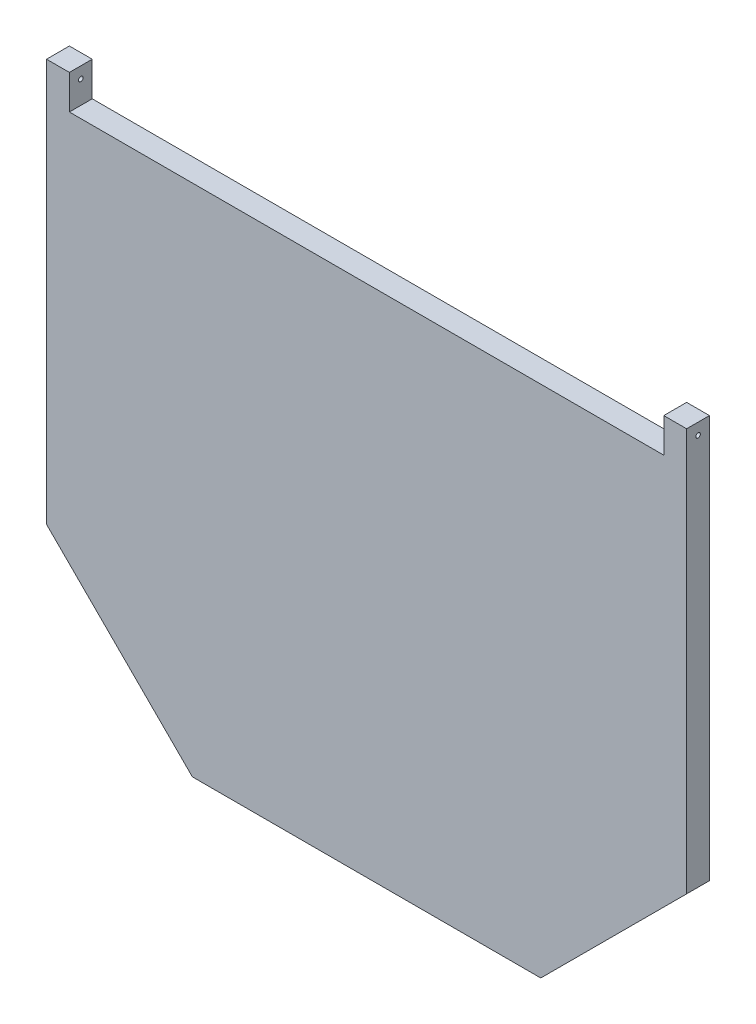
SolidWorks part; units mm, degrees
ref_plane "Front" through (0, 0, 0) normal (0, 0, 1) x (1, 0, 0)
ref_plane "Top" through (0, 0, 0) normal (0, 1, 0) x (1, 0, 0)
ref_plane "Right" through (0, 0, 0) normal (1, 0, 0) x (0, 0, -1)
sketch "Sketch1" plane through (0, 0, 0) normal (0, 0, 1) x (1, 0, 0)
  line L8 (0, 0) -> (355.6, 0)
  line L10 (0, 0) -> (0, -223.774)
  line L11 (0, -223.774) -> (81.026, -304.7518)
  line L12 (81.026, -304.7518) -> (274.574, -304.7518)
  line L13 (274.574, -304.7518) -> (355.6, -223.774)
  line L14 (355.6, -223.774) -> (355.6, 0)
  dimension "D1" = 223.774
  dimension "D2" = 355.6
  dimension "D3" = 114.554
  dimension "D4" = 193.548
extrude "Boss-Extrude1" add sketch "Sketch1" along normal blind 12.7
sketch "Sketch2" plane through (0, 0, 12.7) normal (0, 0, 1) x (1, 0, 0)
  line L6 (355.6, 0) -> (0, 0) construction
  line L7 (12.7, 0) -> (342.9, 0)
  line L8 (12.7, 0) -> (12.7, -19.05)
  line L9 (12.7, -19.05) -> (342.9, -19.05)
  line L10 (342.9, 0) -> (342.9, -19.05)
  line L11 (355.6, -223.774) -> (355.6, 0) construction
  dimension "D1" = 19.05
  dimension "D2" = 330.2
  dimension "D3" = 12.7
extrude "Cut-Extrude1" cut sketch "Sketch2" against normal through all
sketch "Sketch3" plane through (0, 0, 0) normal (-1, 0, 0) x (0, 0, 1)
  line L0 (12.7, 0) -> (12.7, -223.774) construction
  line L1 (12.7, 0) -> (0, 0) construction
  circle A0 centre (6.35, -6.35) radius 1.27
  dimension "D1" = 2.54
  dimension "D2" = 6.35
  dimension "D3" = 6.35
extrude "Cut-Extrude2" cut sketch "Sketch3" against normal through all
sketch "Sketch4" plane through (0, 0, 0) normal (0, 0, 1) x (1, 0, 0)
  line L0 (0, -45.974) -> (0, -223.774) construction
  line L1 (0, 0) -> (0, -223.774) construction
  line L2 (0, -223.774) -> (81.026, -304.7518) construction
  line L3 (81.026, -304.7518) -> (274.574, -304.7518) construction
  line L4 (274.574, -304.7518) -> (355.6, -223.774) construction
  line L5 (355.6, -223.774) -> (355.6, -45.974) construction
  line L6 (355.6, -223.774) -> (355.6, 0) construction
  line L7 (10.3378, -45.974) -> (10.3378, -219.4901)
  line L8 (10.3378, -219.4901) -> (85.3063, -294.414)
  line L10 (270.2937, -294.414) -> (345.2622, -219.4901)
  line L11 (345.2622, -219.4901) -> (345.2622, -45.974)
  line L12 (81.026, -304.7518) -> (85.3063, -294.414) construction
  line L13 (274.574, -304.7518) -> (270.2937, -294.414) construction
  line L14 (0, -223.774) -> (46191.1305, 18917.2674) construction
  line L15 (355.6, -223.774) -> (-45835.5305, 18917.2674) construction
  line L16 (10.3378, -45.974) -> (12.5203, -45.974)
  line L17 (12.5203, -45.974) -> (12.5203, -218.5857)
  line L18 (12.5203, -218.5857) -> (86.2099, -292.2315)
  line L19 (86.2099, -292.2315) -> (85.3063, -294.414)
  line L20 (345.2622, -45.974) -> (342.9, -45.974)
  line L21 (342.9, -45.974) -> (342.9, -218.5113)
  line L22 (342.9, -218.5113) -> (269.4163, -292.2949)
  line L23 (269.4163, -292.2949) -> (270.2937, -294.414)
  line L25 (85.3063, -294.414) -> (270.2937, -294.414) construction
  dimension "D2" = 177.8
  dimension "D3" = 177.8
  dimension "D4" = 2.3622
  dimension "D5" = 2.2936
  dimension "D6" = 2.3622
  dimension "D1" = 10.3378
extrude "Cut-Extrude7" cut sketch "Sketch4" along normal blind 6.35 contours L8 L7 L16 L17 L18 L19 | L10 L11 L20 L21 L22 L23
